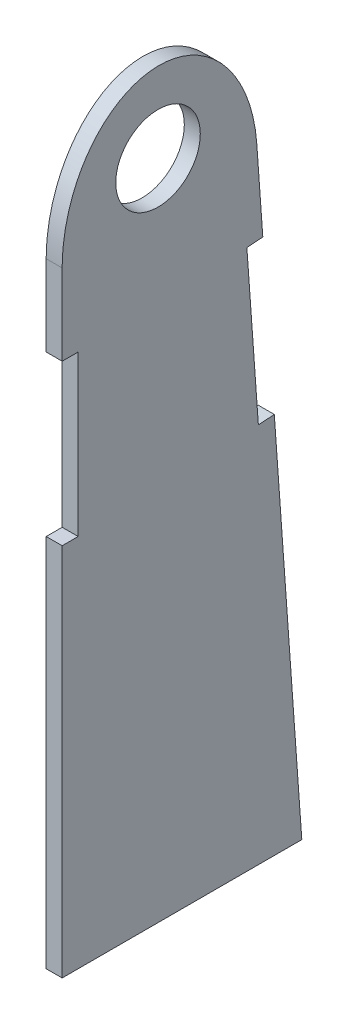
SolidWorks part; units mm, degrees
material "AISI 4130 Steel, annealed at 865C"
ref_plane "X-Y Datum" through (0, 0, 0) normal (0, 0, 1) x (1, 0, 0)
ref_plane "X-Z Datum" through (0, 0, 0) normal (0, 1, 0) x (1, 0, 0)
ref_plane "Y-Z Datum" through (0, 0, 0) normal (1, 0, 0) x (0, 0, -1)
sketch "Sketch1" plane through (0, 0, 0) normal (1, 0, 0) x (0, 0, -1)
  line L0 (0, -65.7746) -> (-9.525, -65.7746)
  line L1 (-9.525, -65.7746) -> (-9.525, 0)
  line L2 (0, -65.7746) -> (14.2875, -65.7746)
  line L3 (14.2875, -65.7746) -> (9.5004, 0.6843)
  line L4 (0, -65.7746) -> (0, 0) construction
  line L5 (-9.525, -28.575) -> (-7.9375, -28.575)
  line L10 (-9.525, -28.575) -> (-9.525, -12.7)
  line L11 (-7.9375, -28.575) -> (-7.9375, -12.7)
  line L12 (-9.525, -12.7) -> (-7.9375, -12.7)
  line L13 (11.5534, -27.8168) -> (10.4128, -11.9829)
  line L14 (11.5534, -27.8168) -> (9.97, -27.9309)
  line L15 (10.4128, -11.9829) -> (8.8294, -12.0969)
  line L16 (9.97, -27.9309) -> (8.8294, -12.0969)
  arc A0 (9.5004, 0.6843) -> (-9.525, 0) centre (0, 0) ccw
  dimension "D1" = 9.525
  dimension "D2" = 14.2875
  dimension "D3" = 9.525
  dimension "D4" = 65.7746
  dimension "D5" = 1.5875
  dimension "D6" = 15.875
  dimension "D7" = 12.7
  dimension "D8" = 12.7
extrude "Boss-Extrude1" add sketch "Sketch1" along normal blind 1.5875
hole_wizard "M8 Clearance Hole1" positions "Sketch2" profile "Sketch3" hole size "M8" standard "ANSI Metric" end condition through all
sketch "Sketch2" plane through (1.5875, 0, 0) normal (1, 0, 0) x (0, 0, -1)
  point P0 (0, 0)
sketch "Sketch3" plane through (1.5875, 0, 0) normal (0, 1, 0) x (0, 0, -1)
  line L0 (0, 0) -> (0, 1.5875)
  line L1 (0, 1.5875) -> (4.2, 1.5875)
  line L2 (4.2, 1.5875) -> (4.2, 0)
  line L5 (4.2, 0) -> (0, 0)
  line L11 (0, -6.35) -> (0, 107.95) construction
  dimension "Thru Hole Dia." = 8.4
  dimension "Thru Hole Depth" = 1.5875
sketch "Sketch4" plane through (1.5875, 0, 0) normal (1, 0, 0) x (0, 0, -1)
  line L2 (10.4128, -11.9829) -> (9.5004, 0.6843) construction
  line L3 (-9.525, -12.7) -> (-9.525, 0) construction
  line L5 (9.8132, -3.6584) -> (9.5004, 0.6843)
  line L6 (-9.525, -4.6718) -> (-9.525, 0)
  arc A3 (9.5004, 0.6843) -> (-9.525, 0) centre (0, 0) ccw construction
  arc A4 (9.5004, 0.6843) -> (-9.525, 0) centre (0, 0) ccw
  ellipse E0 centre (0.1656, -4.7625) end of major axis (0.3311, -17.4625) minor radius 9.69 (9.8132, -3.6584) -> (-9.525, -4.6718) ccw
  point P7 (0, 7.9375)
  dimension "D1" = 7.9375
  dimension "D2" = 4.7625
extrude "Cut-Extrude1" cut sketch "Sketch4" against normal through all
equation "\"D8@Sketch1\"=\"D7@Sketch1\""
